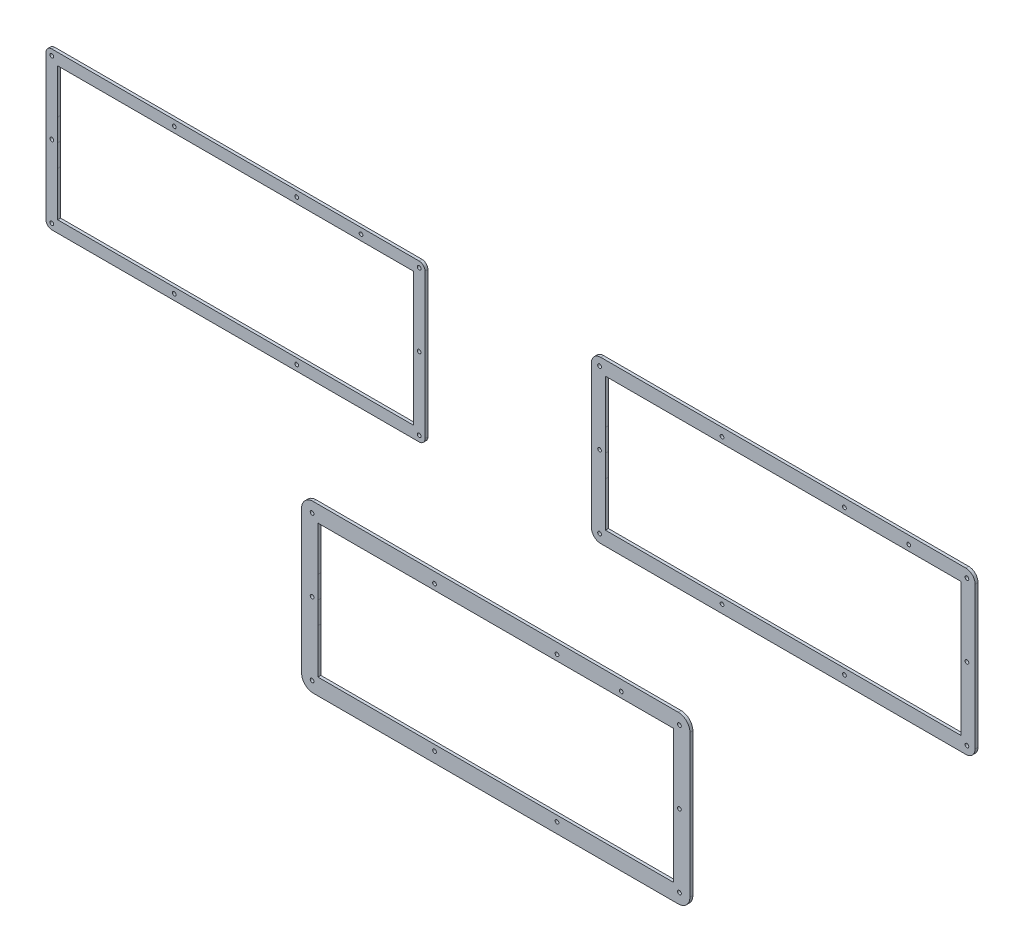
SolidWorks part; units mm, degrees
ref_plane "前视基准面" through (0, 0, 0) normal (0, 0, 1) x (1, 0, 0)
ref_plane "上视基准面" through (0, 0, 0) normal (0, 1, 0) x (1, 0, 0)
ref_plane "右视基准面" through (0, 0, 0) normal (1, 0, 0) x (0, 0, -1)
sketch "草图3" plane through (0, 0, 0) normal (0, 0, 1) x (1, 0, 0)
  line L0 (233.0295, 354.2084) -> (233.0295, 316.1053)
  line L1 (452.0733, 140.3423) -> (764.8752, 140.3423)
  line L2 (442.0733, 130.3423) -> (442.0733, 8.0403)
  line L3 (452.0733, -1.9597) -> (764.8752, -1.9597)
  line L4 (456.0714, 126.3443) -> (456.0714, 88.2412)
  line L5 (456.0714, 88.2412) -> (456.0728, 88.2412)
  line L6 (456.0728, 88.2412) -> (456.0728, 69.1926)
  line L7 (456.0728, 69.1926) -> (456.0714, 69.1926)
  line L8 (456.0714, 69.1926) -> (456.0714, 50.1412)
  line L9 (456.0714, 50.1412) -> (456.0728, 50.1412)
  line L10 (456.0728, 50.1412) -> (456.0728, 12.0411)
  line L11 (456.0728, 12.0411) -> (760.8742, 12.0411)
  line L12 (760.8742, 12.0411) -> (760.8742, 126.3443)
  line L13 (760.8742, 126.3443) -> (456.0714, 126.3443)
  line L14 (774.8752, 130.3423) -> (774.8752, 8.0403)
  line L15 (448.0733, 134.3423) -> (768.8752, 134.3423) construction
  line L16 (448.0733, 134.3423) -> (448.0733, 4.0403) construction
  line L17 (448.0733, 4.0403) -> (768.8752, 4.0403) construction
  line L18 (768.8752, 134.3423) -> (768.8752, 4.0403) construction
  line L19 (233.0295, 316.1053) -> (233.0309, 316.1053)
  line L21 (233.0309, 316.1053) -> (233.0309, 297.0567)
  line L22 (233.0309, 297.0567) -> (233.0295, 297.0567)
  line L23 (233.0295, 297.0567) -> (233.0295, 278.0053)
  line L24 (233.0295, 278.0053) -> (233.0309, 278.0053)
  line L25 (233.0309, 278.0053) -> (233.0309, 239.9052)
  line L26 (233.0309, 239.9052) -> (537.8323, 239.9052)
  line L27 (537.8323, 239.9052) -> (537.8323, 354.2084)
  line L28 (537.8323, 354.2084) -> (233.0295, 354.2084)
  line L29 (225.0314, 362.2064) -> (545.8333, 362.2064) construction
  line L30 (225.0314, 362.2064) -> (225.0314, 231.9043) construction
  line L31 (225.0314, 231.9043) -> (545.8333, 231.9043) construction
  line L32 (545.8333, 362.2064) -> (545.8333, 231.9043) construction
  line L33 (1015.2691, 363.5638) -> (1015.2691, 239.2617) construction
  line L34 (228.0314, 364.2064) -> (542.8333, 364.2064)
  line L35 (223.0314, 359.2064) -> (223.0314, 234.9043)
  line L36 (228.0314, 229.9043) -> (542.8333, 229.9043)
  line L37 (547.8333, 359.2064) -> (547.8333, 234.9043)
  line L38 (1012.2691, 236.2617) -> (697.4672, 236.2617) construction
  line L39 (694.4672, 239.2617) -> (694.4672, 363.5638) construction
  line L40 (697.4672, 366.5638) -> (1012.2691, 366.5638) construction
  line L42 (702.4653, 358.5658) -> (702.4653, 320.4627)
  line L43 (702.4653, 320.4627) -> (702.4667, 320.4627)
  line L44 (702.4667, 320.4627) -> (702.4667, 301.4141)
  line L45 (702.4667, 301.4141) -> (702.4653, 301.4141)
  line L46 (702.4653, 301.4141) -> (702.4653, 282.3627)
  line L47 (702.4653, 282.3627) -> (702.4667, 282.3627)
  line L48 (702.4667, 282.3627) -> (702.4667, 244.2626)
  line L49 (702.4667, 244.2626) -> (1007.2681, 244.2626)
  line L50 (1007.2681, 244.2626) -> (1007.2681, 358.5658)
  line L51 (1007.2681, 358.5658) -> (702.4653, 358.5658)
  line L53 (698.4672, 370.5638) -> (1011.2691, 370.5638)
  line L54 (690.4672, 362.5638) -> (690.4672, 240.2617)
  line L55 (698.4672, 232.2617) -> (1011.2691, 232.2617)
  line L56 (1019.2691, 362.5638) -> (1019.2691, 240.2617)
  circle A11 centre (660.9402, 131.3423) radius 1.6
  circle A12 centre (716.0082, 131.3423) radius 1.6
  circle A13 centre (765.8752, 131.3423) radius 1.6
  circle A14 centre (765.8752, 69.1912) radius 1.5998
  circle A15 centre (765.8752, 7.0402) radius 1.5999
  circle A16 centre (660.9402, 7.0402) radius 1.5999
  circle A17 centre (556.0072, 7.0402) radius 1.5999
  circle A18 centre (451.0733, 7.0402) radius 1.5999
  circle A19 centre (451.0733, 69.1912) radius 1.5998
  circle A20 centre (451.0733, 131.3423) radius 1.6
  circle A21 centre (556.0072, 131.3423) radius 1.6
  arc A26 (764.8752, 140.3423) -> (774.8752, 130.3423) centre (764.8752, 130.3423) cw
  arc A27 (764.8752, -1.9597) -> (774.8752, 8.0403) centre (764.8752, 8.0403) ccw
  arc A28 (442.0733, 8.0403) -> (452.0733, -1.9597) centre (452.0733, 8.0403) ccw
  arc A29 (452.0733, 140.3423) -> (442.0733, 130.3423) centre (452.0733, 130.3423) ccw
  circle A30 centre (437.8983, 359.2064) radius 1.6
  circle A31 centre (492.9663, 359.2064) radius 1.6
  circle A32 centre (542.8333, 359.2064) radius 1.6
  circle A33 centre (542.8333, 297.0553) radius 1.5998
  circle A34 centre (542.8333, 234.9043) radius 1.5999
  circle A35 centre (437.8983, 234.9043) radius 1.5999
  circle A36 centre (332.9653, 234.9043) radius 1.5999
  circle A37 centre (228.0314, 234.9043) radius 1.5999
  circle A38 centre (228.0314, 297.0553) radius 1.5998
  circle A39 centre (228.0314, 359.2064) radius 1.6
  circle A40 centre (332.9653, 359.2064) radius 1.6
  arc A41 (228.0314, 364.2064) -> (223.0314, 359.2064) centre (228.0314, 359.2064) ccw
  arc A42 (223.0314, 234.9043) -> (228.0314, 229.9043) centre (228.0314, 234.9043) ccw
  arc A43 (542.8333, 229.9043) -> (547.8333, 234.9043) centre (542.8333, 234.9043) ccw
  arc A44 (542.8333, 364.2064) -> (547.8333, 359.2064) centre (542.8333, 359.2064) cw
  circle A45 centre (907.3341, 363.5638) radius 1.6
  circle A46 centre (962.4021, 363.5638) radius 1.6
  circle A47 centre (1012.2691, 363.5638) radius 1.6
  circle A48 centre (1012.2691, 301.4127) radius 1.5998
  circle A49 centre (1012.2691, 239.2617) radius 1.5999
  circle A50 centre (907.3341, 239.2617) radius 1.5999
  circle A51 centre (802.4011, 239.2617) radius 1.5999
  circle A52 centre (697.4672, 239.2617) radius 1.5999
  circle A53 centre (697.4672, 301.4127) radius 1.5998
  circle A54 centre (697.4672, 363.5638) radius 1.6
  circle A55 centre (802.4011, 363.5638) radius 1.6
  arc A56 (1011.2691, 370.5638) -> (1019.2691, 362.5638) centre (1011.2691, 362.5638) cw
  arc A57 (1011.2691, 232.2617) -> (1019.2691, 240.2617) centre (1011.2691, 240.2617) ccw
  arc A58 (690.4672, 240.2617) -> (698.4672, 232.2617) centre (698.4672, 240.2617) ccw
  arc A59 (698.4672, 370.5638) -> (690.4672, 362.5638) centre (698.4672, 362.5638) ccw
  point P0 (0, 0)
  point P182 (0, 0)
  dimension "D5" = 3.2
  dimension "D14" = 10
  dimension "D15" = 3.2
  dimension "D17" = 5
  dimension "D21" = 5
  dimension "D22" = 3.2
  dimension "D26" = 4
  dimension "D30" = 8
  dimension "D6" = 55.068
  dimension "D7" = 304.8028
  dimension "D8" = 114.3032
  dimension "D10" = 6
  dimension "D11" = 6
  dimension "D12" = 6
  dimension "D13" = 6
  dimension "D16" = 2
  dimension "D18" = 2
  dimension "D19" = 2
  dimension "D20" = 2
  dimension "D23" = 55.068
  dimension "D24" = 304.8028
  dimension "D25" = 114.3032
  dimension "D27" = 4
  dimension "D28" = 4
  dimension "D29" = 4
extrude "凸台-拉伸2" add sketch "草图3" along normal blind 2.5 contours L27 L28 L0 L19 L21 L22 L23 L24 L25 L26 | L12 L13 L4 L5 L6 L7 L8 L9 L10 L11 | L50 L51 L42 L43 L44 L45 L46 L47 L48 L49 | L34 A44 L37 A43 L36 A42 L35 A41 | L53 A56 L56 A57 L55 A58 L54 A59 | L1 A26 L14 A27 L3 A28 L2 A29 | A34 | A33 | A32 | A31 | A30 | A40 | A39 | A38 | A37 | A36 | A35 | A18 | A19 | A20 | A21 | A11 | A12 | A13 | A14 | A15 | A16 | A17 | A52 | A53 | A54 | A55 | A45 | A51 | A50 | A49 | A48 | A47 | A46
